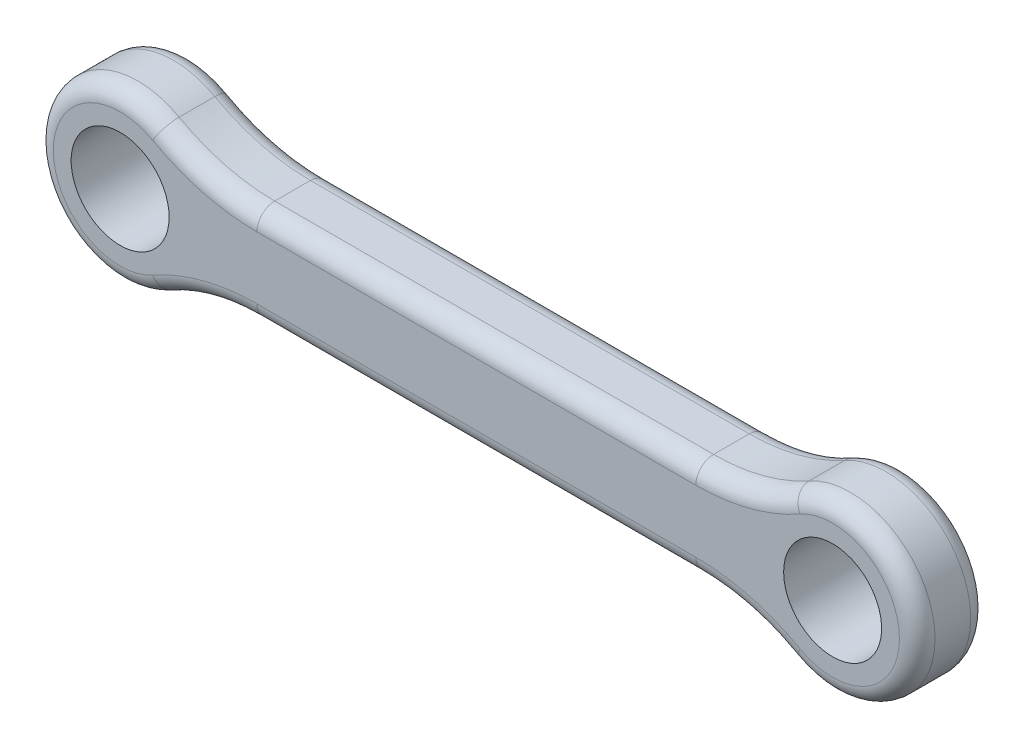
SolidWorks part; units mm, degrees
ref_plane "Front Plane" through (0, 0, 0) normal (0, 0, 1) x (1, 0, 0)
ref_plane "Top Plane" through (0, 0, 0) normal (0, 1, 0) x (1, 0, 0)
ref_plane "Right Plane" through (0, 0, 0) normal (1, 0, 0) x (0, 0, -1)
sketch "Sketch1" plane through (0, 0, 0) normal (0, 0, 1) x (1, 0, 0)
  line L0 (0, -55) -> (0, 55) construction
  line L2 (-12.3189, -2.75) -> (12.3189, -2.75)
  line L3 (-12.3189, 2.75) -> (12.3189, 2.75)
  circle A0 centre (-20, 0) radius 2.75
  arc A1 (-17.6835, 4.1468) -> (-17.6835, -4.1468) centre (-20, 0) ccw
  arc A2 (-12.3189, -2.75) -> (-17.6835, -4.1468) centre (-12.3189, -13.75) ccw
  circle A3 centre (-20, 0) radius 4.75 construction
  arc A4 (-12.3189, 2.75) -> (-17.6835, 4.1468) centre (-12.3189, 13.75) cw
  arc A5 (12.3189, -2.75) -> (17.6835, -4.1468) centre (12.3189, -13.75) cw
  arc A6 (12.3189, 2.75) -> (17.6835, 4.1468) centre (12.3189, 13.75) ccw
  circle A7 centre (20, 0) radius 2.75
  arc A8 (17.6835, 4.1468) -> (17.6835, -4.1468) centre (20, 0) cw
  point P7 (-15.25, 0)
  point P19 (0, -2.75)
  point P20 (0, 2.75)
  dimension "D1" = 5.5
  dimension "D4" = 11
  dimension "D2" = 20
  dimension "D3" = 2
extrude "Boss-Extrude1" add sketch "Sketch1" along normal blind 4 contours A5 A8 A6 L3 A4 A1 A2 L2 | A0 | A7
fillet "Fillet1" radius 1 16 edges at (-15.0906, 3.1049, 4) (-24.75, 0, 4) (-15.0906, -3.1049, 4) (0, -2.75, 4) (15.0906, -3.1049, 4) (24.75, 0, 4) (15.0906, 3.1049, 4) (-15.0906, 3.1049, 0) (-24.75, 0, 0) (-15.0906, -3.1049, 0) (0, -2.75, 0) (15.0906, -3.1049, 0) (24.75, 0, 0) (15.0906, 3.1049, 0) (0, 2.75, 4) (0, 2.75, 0)
